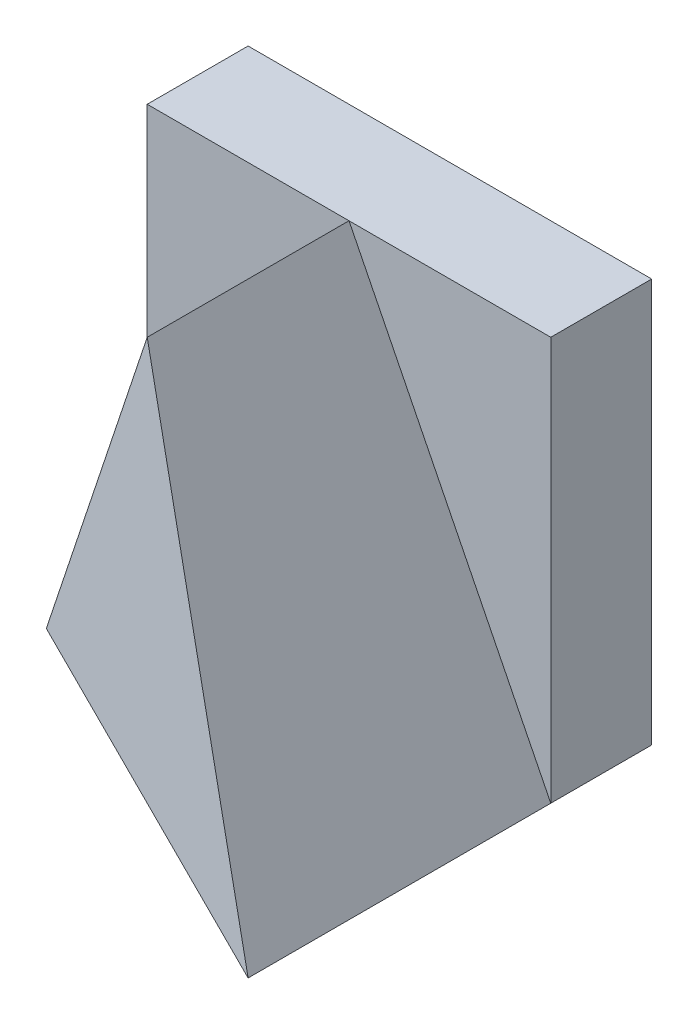
SolidWorks part; units mm, degrees
ref_plane "Front" through (0, 0, 0) normal (0, 0, 1) x (1, 0, 0)
ref_plane "Top" through (0, 0, 0) normal (0, 1, 0) x (1, 0, 0)
ref_plane "Right" through (0, 0, 0) normal (1, 0, 0) x (0, 0, -1)
sketch "Sketch2" plane through (0, 0, 0) normal (0, 1, 0) x (1, 0, 0)
  line L1 (-2, -2) -> (2, -2)
  line L2 (-2, -2) -> (-2, 2)
  line L3 (-2, 2) -> (2, 2)
  line L4 (2, -2) -> (2, 2)
  line L5 (-2, -2) -> (2, 2) construction
  line L6 (-2, 2) -> (2, -2) construction
  point P0 (0, 0)
  dimension "D1" = 4
  dimension "D2" = 4
extrude "Boss-Extrude1" add sketch "Sketch2" along normal blind 4
sketch "Sketch3" plane through (0, 0, 2) normal (0, 0, 1) x (1, 0, 0)
  line L0 (-2, 0) -> (-2, 4)
  line L1 (-2, 4) -> (2, 4)
  line L2 (2, 4) -> (2, 0)
  line L3 (2, 0) -> (0, 4)
  line L4 (0, 4) -> (-2, 0)
  line M2 (2, 0) -> (2, 4)
  line M3 (2, 4) -> (-2, 4)
  line M4 (-2, 4) -> (-2, 0)
extrude "Cut-Extrude1" cut sketch "Sketch3" against normal blind 3 contours L3 M2 M3 | L4 L1 M4
sketch "Sketch4" plane through (0, 0, 0) normal (0, -1, 0) x (1, 0, 0)
  line L0 (2, 2) -> (-2, 0)
  line L1 (-2, -1) -> (-2, 2) construction
  line L2 (-2, 0) -> (-2, 2)
  line L3 (-2, 2) -> (2, 2)
  dimension "D1" = 2
extrude "Cut-Extrude2" cut sketch "Sketch4" against normal blind 7
